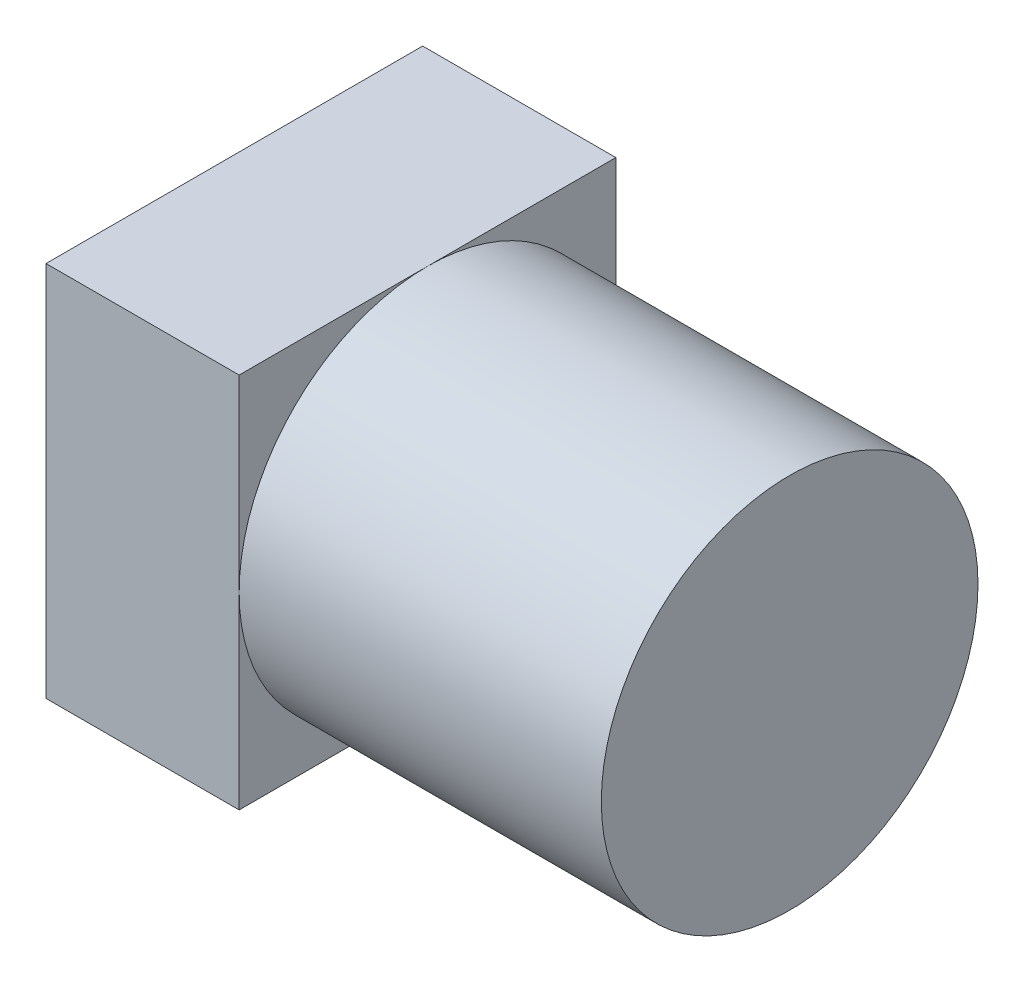
SolidWorks part; units mm, degrees
ref_plane "Front Plane" through (0, 0, 0) normal (0, 0, 1) x (1, 0, 0)
ref_plane "Top Plane" through (0, 0, 0) normal (0, 1, 0) x (1, 0, 0)
ref_plane "Right Plane" through (0, 0, 0) normal (1, 0, 0) x (0, 0, -1)
sketch "Sketch1" plane through (0, 0, 0) normal (1, 0, 0) x (0, 0, -1)
  line L1 (-7.8, 7.8) -> (7.8, 7.8)
  line L2 (-7.8, 7.8) -> (-7.8, -7.8)
  line L3 (-7.8, -7.8) -> (7.8, -7.8)
  line L4 (7.8, 7.8) -> (7.8, -7.8)
  line L5 (-7.8, 7.8) -> (7.8, -7.8) construction
  line L6 (-7.8, -7.8) -> (7.8, 7.8) construction
  point P0 (0, 0)
  dimension "D1" = 15.6
  dimension "D2" = 15.6
extrude "Boss-Extrude1" add sketch "Sketch1" along normal blind 8
sketch "Sketch2" plane through (8, 0, 0) normal (1, 0, 0) x (0, 0, -1)
  circle A0 centre (0, 0) radius 7.8
  dimension "D1" = 15.6
extrude "Boss-Extrude2" add sketch "Sketch2" along normal blind 15
